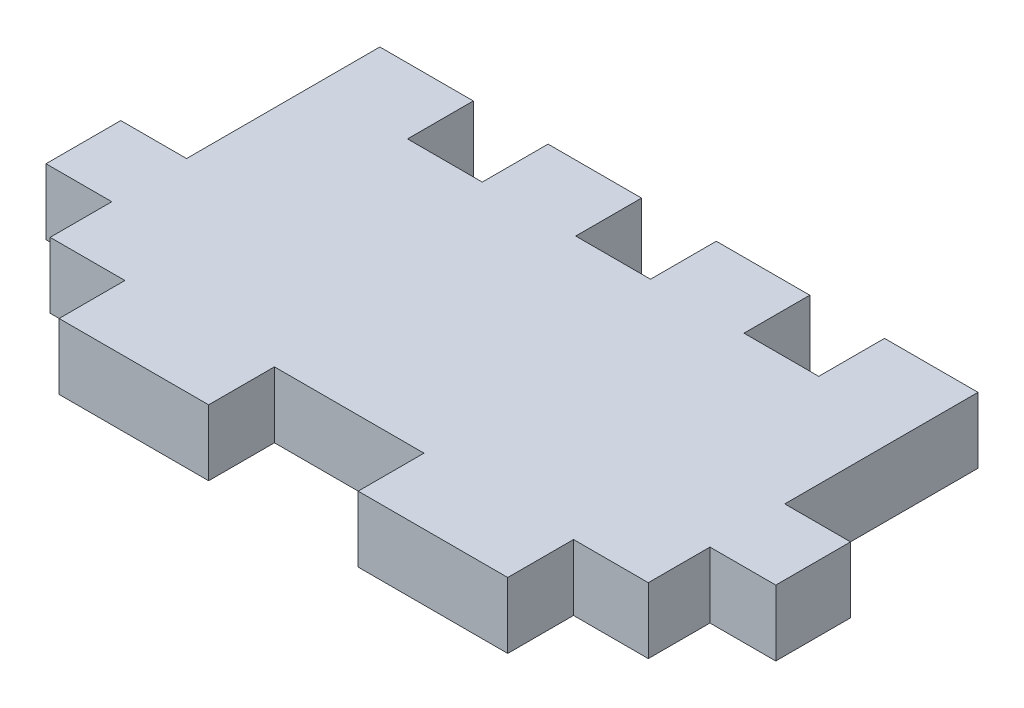
SolidWorks part; units mm, degrees
material "Acrylic (Medium-high impact)"
ref_plane "Front Plane" through (0, 0, 0) normal (0, 0, 1) x (1, 0, 0)
ref_plane "Top Plane" through (0, 0, 0) normal (0, 1, 0) x (1, 0, 0)
ref_plane "Right Plane" through (0, 0, 0) normal (1, 0, 0) x (0, 0, -1)
sketch "Sketch1" plane through (0, 0, 0) normal (0, 1, 0) x (1, 0, 0)
  line L0 (-11.1125, 14) -> (-3.175, 14) construction
  line L1 (-30.988, 16.794) -> (30.988, 16.794)
  line L2 (-30.988, 16.794) -> (-30.988, -16.794)
  line L3 (-30.988, -16.794) -> (30.988, -16.794)
  line L4 (30.988, 16.794) -> (30.988, -16.794)
  line L5 (-30.988, 16.794) -> (30.988, -16.794) construction
  line L6 (-30.988, -16.794) -> (30.988, 16.794) construction
  line L7 (-30.988, -11.206) -> (-19.05, -11.206)
  line L8 (-30.988, -11.206) -> (-30.988, -16.794)
  line L9 (-30.988, -16.794) -> (-19.05, -16.794)
  line L10 (-19.05, -11.206) -> (-19.05, -16.794)
  line L11 (30.988, -11.206) -> (19.05, -11.206)
  line L12 (30.988, -11.206) -> (30.988, -16.794)
  line L13 (30.988, -16.794) -> (19.05, -16.794)
  line L14 (19.05, -11.206) -> (19.05, -16.794)
  line L15 (-6.35, -16.794) -> (6.35, -16.794)
  line L16 (-6.35, -16.794) -> (-6.35, -11.206)
  line L17 (-6.35, -11.206) -> (6.35, -11.206)
  line L18 (6.35, -16.794) -> (6.35, -11.206)
  line L19 (25.4, 16.794) -> (30.988, 16.794)
  line L20 (25.4, 16.794) -> (25.4, 0.381)
  line L21 (25.4, 0.381) -> (30.988, 0.381)
  line L22 (30.988, 16.794) -> (30.988, 0.381)
  line L23 (-25.4, 16.794) -> (-30.988, 16.794)
  line L24 (-25.4, 16.794) -> (-25.4, 0.381)
  line L25 (-25.4, 0.381) -> (-30.988, 0.381)
  line L26 (-30.988, 16.794) -> (-30.988, 0.381)
  line L39 (-17.4625, 16.794) -> (-11.1125, 16.794)
  line L40 (-17.4625, 16.794) -> (-17.4625, 11.206)
  line L41 (-17.4625, 11.206) -> (-11.1125, 11.206)
  line L42 (-11.1125, 16.794) -> (-11.1125, 11.206)
  line L43 (-3.175, 16.794) -> (3.175, 16.794)
  line L44 (-3.175, 16.794) -> (-3.175, 11.206)
  line L45 (-3.175, 11.206) -> (3.175, 11.206)
  line L46 (3.175, 16.794) -> (3.175, 11.206)
  line L47 (11.1125, 16.794) -> (17.4625, 16.794)
  line L48 (11.1125, 16.794) -> (11.1125, 11.206)
  line L49 (11.1125, 11.206) -> (17.4625, 11.206)
  line L50 (17.4625, 16.794) -> (17.4625, 11.206)
  line L51 (-17.4625, 14) -> (-25.4, 14) construction
  line L52 (3.175, 14) -> (11.1125, 14) construction
  line L53 (17.4625, 14) -> (25.4, 14) construction
  line L55 (-30.988, -16.794) -> (-25.4, -16.794)
  line L56 (-30.988, -16.794) -> (-30.988, -5.969)
  line L57 (-30.988, -5.969) -> (-25.4, -5.969)
  line L58 (-25.4, -16.794) -> (-25.4, -5.969)
  line L59 (30.988, -16.794) -> (25.4, -16.794)
  line L60 (30.988, -16.794) -> (30.988, -5.969)
  line L61 (30.988, -5.969) -> (25.4, -5.969)
  line L62 (25.4, -16.794) -> (25.4, -5.969)
  point P0 (0, 0)
  point P22 (0, -11.206)
  point P35 (0, 11.206)
  dimension "D1" = 61.976
  dimension "D2" = 33.588
  dimension "D3" = 5.588
  dimension "D4" = 12.7
  dimension "D5" = 12.7
  dimension "D6" = 12.7
  dimension "D7" = 5.588
  dimension "D8" = 16.413
  dimension "D9" = 6.35
  dimension "D10" = 10.825
  dimension "D11" = 5.588
extrude "Boss-Extrude1" add sketch "Sketch1" along normal blind 5.588 contours L1 L50 L49 L48 L46 L45 L44 L42 L41 L40 L24 L25 L2 L7 L10 L3 L16 L17 L18 L14 L11 L4 L21 L20
